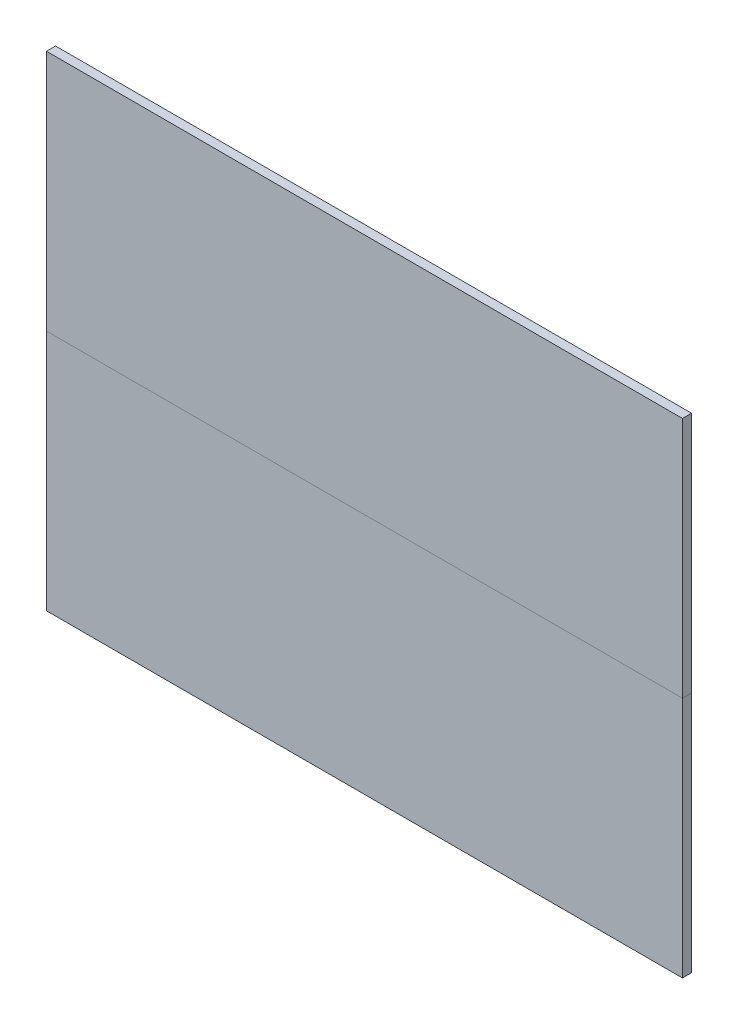
SolidWorks part; units mm, degrees
ref_plane "Alzado" through (0, 0, 0) normal (0, 0, 1) x (1, 0, 0)
ref_plane "Planta" through (0, 0, 0) normal (0, 1, 0) x (1, 0, 0)
ref_plane "Vista lateral" through (0, 0, 0) normal (1, 0, 0) x (0, 0, -1)
sketch "Croquis1" plane through (0, 0, 0) normal (0, 0, 1) x (1, 0, 0)
  line L1 (0, 0) -> (21, 0)
  line L2 (0, 0) -> (0, 8)
  line L3 (0, 8) -> (21, 8)
  line L4 (21, 0) -> (21, 8)
  dimension "D1" = 21
  dimension "D2" = 8
extrude "Saliente-Extruir1" add sketch "Croquis1" along normal blind 0.3
sketch "Croquis2" plane through (0, 0, 0.3) normal (0, 0, 1) x (1, 0, 0)
  line L0 (21, 0) -> (21, 8) construction
  line L1 (0, 8) -> (21, 8)
  line L2 (0, 8) -> (0, 16)
  line L3 (0, 16) -> (21, 16)
  line L4 (21, 8) -> (21, 16)
  line L5 (21, 8) -> (0, 8) construction
  dimension "D1" = 8
extrude "Saliente-Extruir2" add sketch "Croquis2" against normal up to surface (0.3 mm away) separate body up to face at (10.5, 4, 0)
